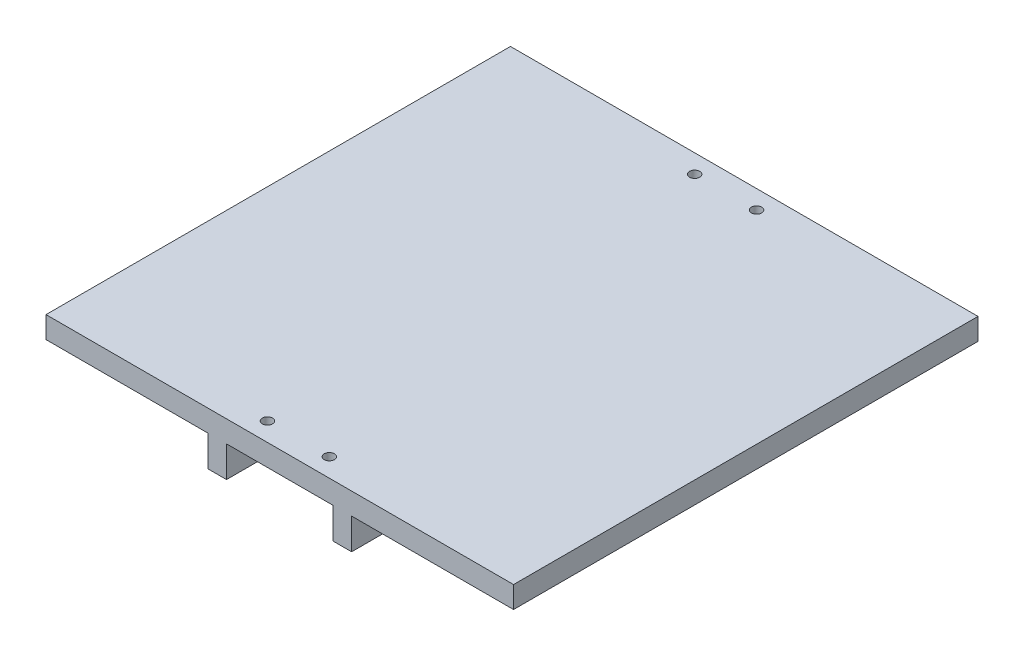
SolidWorks part; units mm, degrees
ref_plane "Front Plane" through (0, 0, 0) normal (0, 0, 1) x (1, 0, 0)
ref_plane "Top Plane" through (0, 0, 0) normal (0, 1, 0) x (1, 0, 0)
ref_plane "Right Plane" through (0, 0, 0) normal (1, 0, 0) x (0, 0, -1)
sketch "Sketch1" plane through (0, 0, 0) normal (0, 0, 1) x (1, 0, 0)
  line L0 (0, 3.5) -> (0, -3.5) construction
  line L1 (-75.5, 3.5) -> (75.5, 3.5)
  line L2 (-75.5, 3.5) -> (-75.5, -3.5)
  line L3 (-75.5, -3.5) -> (-23.2, -3.5)
  line L4 (75.5, 3.5) -> (75.5, -3.5)
  line L5 (-75.5, 3.5) -> (75.5, -3.5) construction
  line L6 (-75.5, -3.5) -> (75.5, 3.5) construction
  line L7 (17.2, -3.5) -> (17.2, -13.5)
  line L8 (17.2, -13.5) -> (23.2, -13.5)
  line L9 (23.2, -13.5) -> (23.2, -3.5)
  line L10 (-23.2, -13.5) -> (-23.2, -3.5)
  line L11 (-17.2, -13.5) -> (-23.2, -13.5)
  line L12 (-17.2, -3.5) -> (-17.2, -13.5)
  line L13 (-17.2, -3.5) -> (17.2, -3.5)
  line L14 (23.2, -3.5) -> (75.5, -3.5)
  point P0 (0, 0)
  dimension "D1" = 7
  dimension "D2" = 151
  dimension "D3" = 6
  dimension "D4" = 10
  dimension "D5" = 23.2
extrude "Boss-Extrude1" add sketch "Sketch1" along normal blind 150
sketch "Sketch4" plane through (0, -3.5, 0) normal (0, -1, 0) x (1, 0, 0)
  line L0 (0, 150) -> (0, 0) construction
  line L1 (-17.2, 150) -> (17.2, 150) construction
  line L2 (-17.2, 144) -> (17.2, 144) construction
  line L3 (-17.2, 150) -> (-17.2, 0) construction
  line L4 (17.2, 150) -> (17.2, 0) construction
  line L5 (-17.2, 6) -> (17.2, 6) construction
  line L6 (-10, 150) -> (-10, 0) construction
  line L7 (-17.2, 0) -> (17.2, 0) construction
  line L8 (10, 150) -> (10, 0) construction
  circle A0 centre (-10, 6) radius 1.65
  circle A1 centre (10, 6) radius 1.65
  circle A2 centre (-10, 144) radius 1.65
  circle A3 centre (10, 144) radius 1.65
  dimension "D4" = 3.3
  dimension "D5" = 3.3
  dimension "D1" = 6
  dimension "D2" = 6
  dimension "D3" = 10
extrude "Cut-Extrude1" cut sketch "Sketch4" against normal up to surface (7 mm away) up to face at (0, 3.5, 75)
